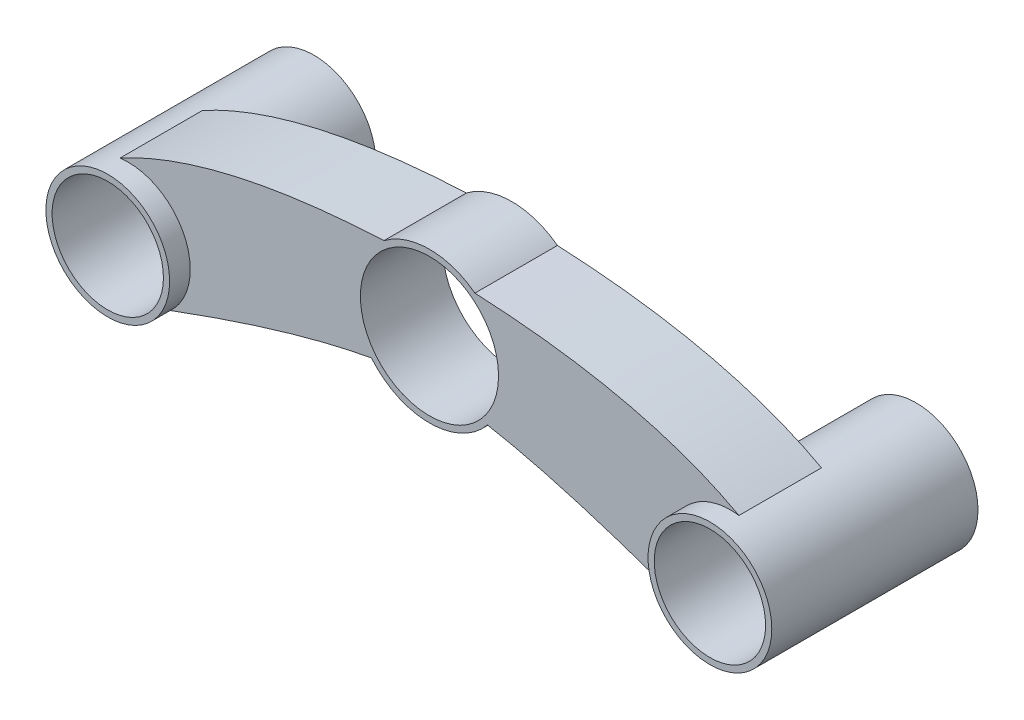
SolidWorks part; units mm, degrees
ref_plane "Front Plane" through (0, 0, 0) normal (0, 0, 1) x (1, 0, 0)
ref_plane "Top Plane" through (0, 0, 0) normal (0, 1, 0) x (1, 0, 0)
ref_plane "Right Plane" through (0, 0, 0) normal (1, 0, 0) x (0, 0, -1)
sketch "Sketch1" plane through (0, 0, 0) normal (0, 0, 1) x (1, 0, 0)
  circle A0 centre (0, 0) radius 13.5
  circle A1 centre (146, 0) radius 13.5
  circle A2 centre (0, 0) radius 15
  circle A3 centre (146, 0) radius 15
  dimension "D2" = 27
  dimension "D3" = 27
  dimension "D4" = 30
  dimension "D5" = 30
  dimension "D1" = 146
extrude "Boss-Extrude1" add sketch "Sketch1" along normal blind 50
ref_plane "Plane1" through (0, 0, 25) normal (0, 0, 1) x (1, 0, 0)
sketch "Sketch2" plane through (0, 0, 25) normal (0, 0, 1) x (1, 0, 0)
  line L0 (0, 0) -> (146, 0) construction
  line L1 (73, 15) -> (73, -24.9898) construction
  arc A0 (58.93, 3.3768) -> (87.07, 3.3768) centre (73, 15) ccw
  circle A1 centre (73, 15) radius 16.75
  circle A2 centre (0, 0) radius 15 construction
  arc A3 (10.1419, -11.0518) -> (-2.0418, 14.8604) centre (0, 0) ccw
  arc A4 (135.8581, -11.0518) -> (148.0418, 14.8604) centre (146, 0) cw
  circle A5 centre (146, 0) radius 15 construction
  arc A6 (84.0249, 29.5435) -> (61.9751, 29.5435) centre (73, 15) ccw
  spline S0 degree 2 poles (-2.0418, 14.8604) (21.2766, 27.6191) (61.9751, 29.5435) knots 0 0 0 1 1 1
  spline S1 degree 2 poles (10.1419, -11.0518) (39.6063, -0.1089) (58.93, 3.3768) knots 0 0 0 1 1 1
  spline S2 degree 2 poles (148.0418, 14.8604) (124.7234, 27.6191) (84.0249, 29.5435) knots 0 0 0 1 1 1
  spline S3 degree 2 poles (135.8581, -11.0518) (106.3937, -0.1089) (87.07, 3.3768) knots 0 0 0 1 1 1
  point P18 (0, 0)
  point P19 (0, 0)
  point P20 (0, 0)
  point P21 (60.0148, 27.8237)
  point P22 (0, 0)
  point P23 (0, 0)
  point P24 (61.9751, 29.5435)
  dimension "D1" = 36.5
  dimension "D2" = 33.5
  dimension "D3" = 15
extrude "Boss-Extrude5" add sketch "Sketch2" along normal blind 20 separate body
